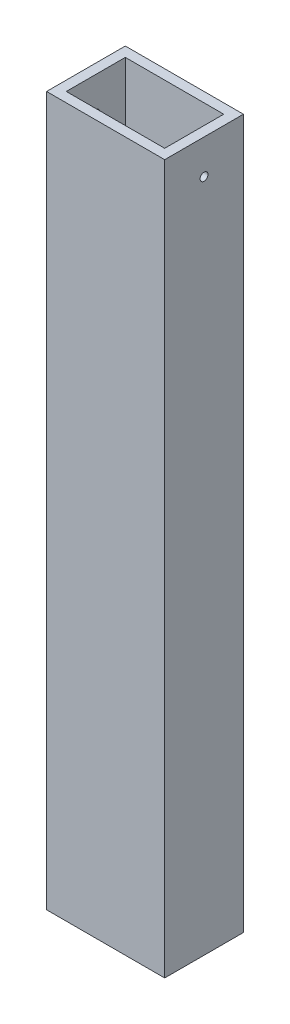
SolidWorks part; units mm, degrees
ref_plane "Front Plane" through (0, 0, 0) normal (0, 0, 1) x (1, 0, 0)
ref_plane "Top Plane" through (0, 0, 0) normal (0, 1, 0) x (1, 0, 0)
ref_plane "Right Plane" through (0, 0, 0) normal (1, 0, 0) x (0, 0, -1)
sketch "Sketch1" plane through (0, 0, 0) normal (0, 1, 0) x (1, 0, 0)
  line L0 (-31.75, -19.05) -> (-31.75, 19.05)
  line L1 (-38.1, -25.4) -> (38.1, -25.4)
  line L2 (-38.1, -25.4) -> (-38.1, 25.4)
  line L3 (-38.1, 25.4) -> (38.1, 25.4)
  line L4 (38.1, -25.4) -> (38.1, 25.4)
  line L5 (-38.1, -25.4) -> (38.1, 25.4) construction
  line L6 (-38.1, 25.4) -> (38.1, -25.4) construction
  line L7 (-31.75, 19.05) -> (31.75, 19.05)
  line L8 (31.75, -19.05) -> (31.75, 19.05)
  line L9 (-31.75, -19.05) -> (31.75, -19.05)
  point P0 (0, 0)
  dimension "D2" = 50.8
  dimension "D3" = 76.2
  dimension "D1" = 6.35
extrude "Boss-Extrude1" add sketch "Sketch1" along normal blind 457.2
sketch "Sketch2" plane through (0, 0, -25.4) normal (0, 0, -1) x (-1, 0, 0)
  line L0 (0, 0) -> (0, 457.2) construction
  line L1 (-38.1, 457.2) -> (38.1, 457.2) construction
  line L2 (35.5, 376.2) -> (-35.5, 376.2)
  line L3 (0, 304.8) -> (-35.5, 376.2)
  line L4 (0, 304.8) -> (35.5, 376.2)
  point P7 (17.75, 340.5)
  point P9 (0, 304.8)
  point P12 (0, 376.2)
  dimension "D1" = 304.8
  dimension "D2" = 35.5
  dimension "D3" = 71.4
sketch "Sketch3" plane through (-38.1, 0, 0) normal (-1, 0, 0) x (0, 0, 1)
  line L0 (0, 457.2) -> (0, 434.975)
  line L1 (-25.4, 457.2) -> (25.4, 457.2) construction
  dimension "D1" = 22.225
hole_wizard "1/4-20 Tapped Hole1" positions "Sketch5" profile "Sketch6" tap size "1/4-20" standard "ANSI Inch" end condition through all
sketch "Sketch5" plane through (-38.1, 0, 0) normal (-1, 0, 0) x (0, 0, 1)
  point P0 (0, 434.975)
sketch "Sketch6" plane through (-38.1, 434.975, 0) normal (0, 1, 0) x (0, 0, 1)
  line L0 (0, 0) -> (0, 76.2)
  line L1 (0, 76.2) -> (2.5527, 76.2)
  line L2 (2.5527, 76.2) -> (2.5527, 0)
  line L5 (2.5527, 0) -> (0, 0)
  line L11 (0, -6.35) -> (0, 107.95) construction
  dimension "Thru Tap Drill Dia." = 5.1054
  dimension "Thru Tap Drill Depth" = 76.2
cosmetic thread "Hole Thread1" parameters "D2"=6.35
